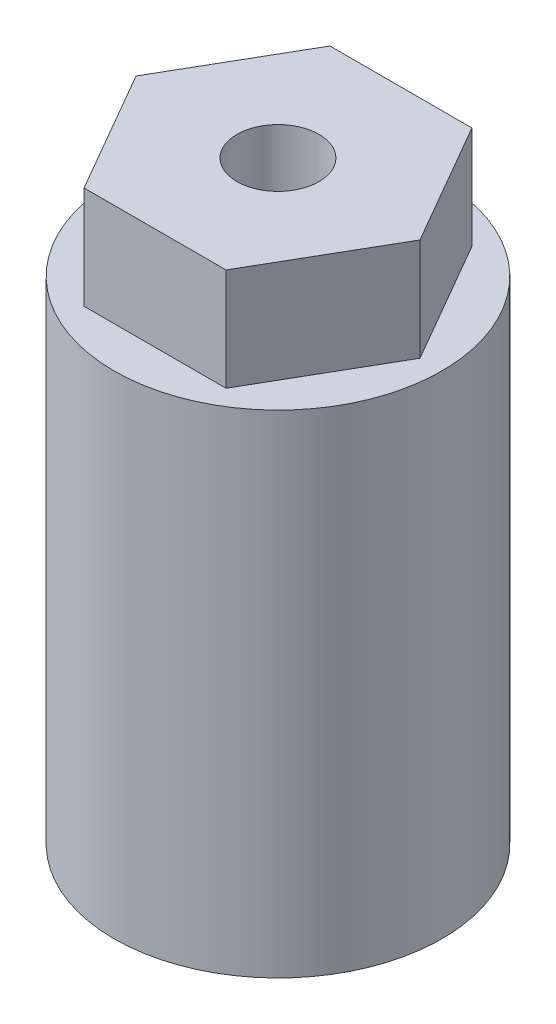
SolidWorks part; units mm, degrees
ref_plane "Front Plane" through (0, 0, 0) normal (0, 0, 1) x (1, 0, 0)
ref_plane "Top Plane" through (0, 0, 0) normal (0, 1, 0) x (1, 0, 0)
ref_plane "Right Plane" through (0, 0, 0) normal (1, 0, 0) x (0, 0, -1)
sketch "Sketch1" plane through (0, 0, 0) normal (0, 0, 1) x (1, 0, 0)
  line L0 (0, 0) -> (0, 16.2128) construction
  line L2 (0, 0) -> (8, 0)
  line L3 (0, 0) -> (0, 12)
  line L4 (0, 12) -> (8, 12)
  line L5 (8, 0) -> (8, 12)
  line L6 (0, 0) -> (4, 0)
  line L7 (0, 0) -> (0, 12)
  line L8 (0, 12) -> (4, 12)
  line L9 (4, 0) -> (4, 12)
  line L10 (8, 12) -> (0, 12)
  line L11 (8, 12) -> (8, 24)
  line L12 (8, 24) -> (0, 24)
  line L13 (0, 12) -> (0, 24)
  dimension "D1" = 12
  dimension "D2" = 4
  dimension "D3" = 4
  dimension "D4" = 12
revolve "Revolve1" add sketch "Sketch1" angle 360 about L0
sketch "Sketch2" plane through (0, 24, 0) normal (0, 1, 0) x (1, 0, 0)
  line L1 (6.9282, 0) -> (3.4641, 6)
  line L2 (3.4641, 6) -> (-3.4641, 6)
  line L3 (-3.4641, 6) -> (-6.9282, 0)
  line L4 (-6.9282, 0) -> (-3.4641, -6)
  line L5 (-3.4641, -6) -> (3.4641, -6)
  line L6 (3.4641, -6) -> (6.9282, 0)
  circle A0 centre (0, 0) radius 6 construction
  dimension "D1" = 12
extrude "Boss-Extrude1" add sketch "Sketch2" along normal blind 5
hole_wizard "Ø4.0mm Dowel Hole1" positions "Sketch3" profile "Sketch4" hole size "Ø4.0" standard "ANSI Metric"
sketch "Sketch3" plane through (0, 29, 0) normal (0, 1, 0) x (1, 0, 0)
  point P0 (0, 0)
sketch "Sketch4" plane through (0, 29, 0) normal (1, 0, 0) x (0, 0, 1)
  line L0 (0, 0) -> (0, 11.2017)
  line L1 (0, 11.2017) -> (2, 10)
  line L2 (2, 10) -> (2, 0)
  line L5 (2, 0) -> (0, 0)
  line L10 (0, 11.2017) -> (-2, 10) construction
  line L11 (0, -6.35) -> (0, 107.95) construction
  dimension "Hole Dia." = 4
  dimension "Hole Depth" = 10
  dimension "Drill Angle" = 118
sketch "Sketch5" plane through (0, 0, 0) normal (0, -1, 0) x (1, 0, 0)
  line L1 (2.5, -1.5) -> (5.5, -1.5)
  line L2 (2.5, -1.5) -> (2.5, 1.5)
  line L3 (2.5, 1.5) -> (5.5, 1.5)
  line L4 (5.5, -1.5) -> (5.5, 1.5)
  line L5 (2.5, -1.5) -> (5.5, 1.5) construction
  line L6 (2.5, 1.5) -> (5.5, -1.5) construction
  circle A0 centre (0, 0) radius 4 construction
  point P0 (4, 0)
  dimension "D1" = 3
  dimension "D2" = 3
extrude "Cut-Extrude1" cut sketch "Sketch5" against normal up to surface (12 mm away)
